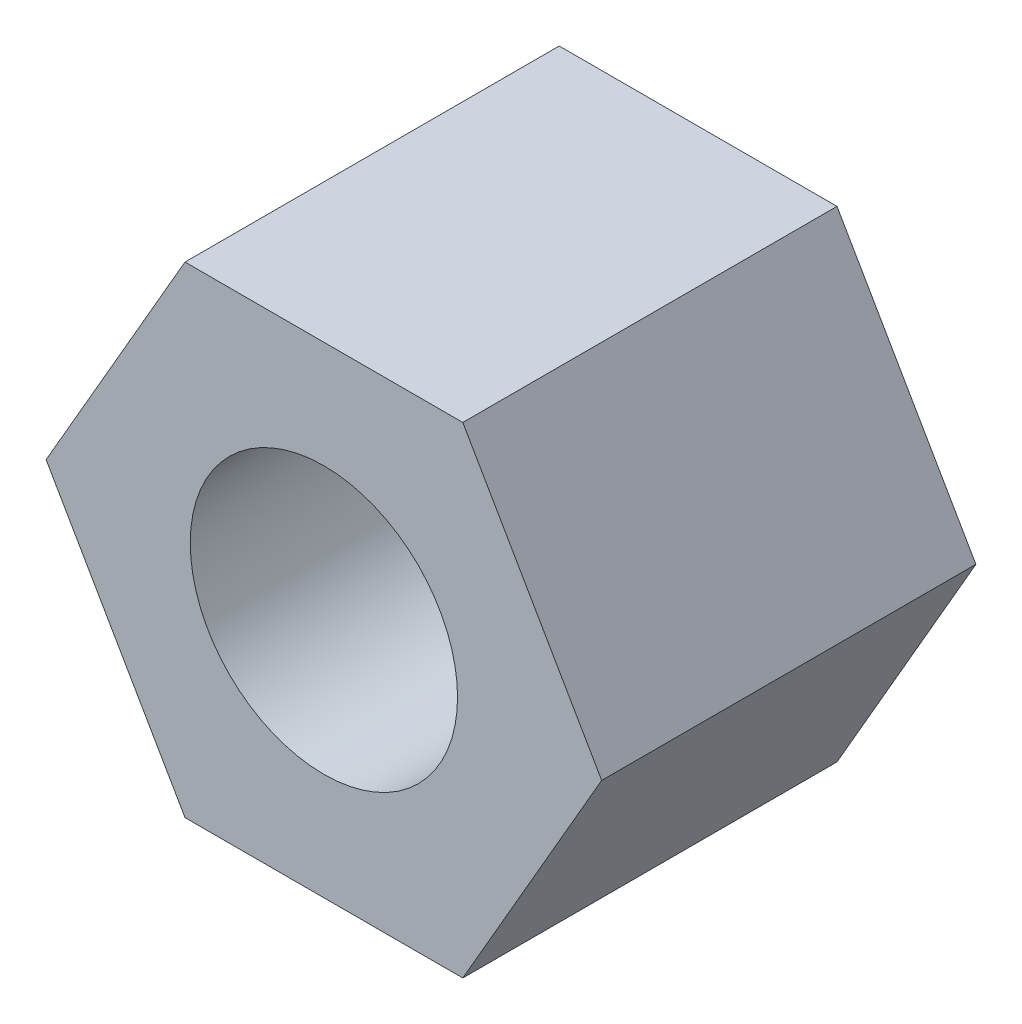
SolidWorks part; units mm, degrees
ref_plane "Front Plane" through (0, 0, 0) normal (0, 0, 1) x (1, 0, 0)
ref_plane "Top Plane" through (0, 0, 0) normal (0, 1, 0) x (1, 0, 0)
ref_plane "Right Plane" through (0, 0, 0) normal (1, 0, 0) x (0, 0, -1)
sketch "Sketch1" plane through (0, 0, 0) normal (0, 0, 1) x (1, 0, 0)
  line L1 (-2.5981, 0) -> (-1.299, -2.25)
  line L2 (-1.299, -2.25) -> (1.299, -2.25)
  line L3 (1.299, -2.25) -> (2.5981, 0)
  line L4 (2.5981, 0) -> (1.299, 2.25)
  line L5 (1.299, 2.25) -> (-1.299, 2.25)
  line L6 (-1.299, 2.25) -> (-2.5981, 0)
  circle A0 centre (0, 0) radius 1.25
  circle A1 centre (0, 0) radius 2.25 construction
  dimension "D1" = 2.5
  dimension "D2" = 4.5
extrude "Boss-Extrude1" add sketch "Sketch1" along normal blind 3.5
